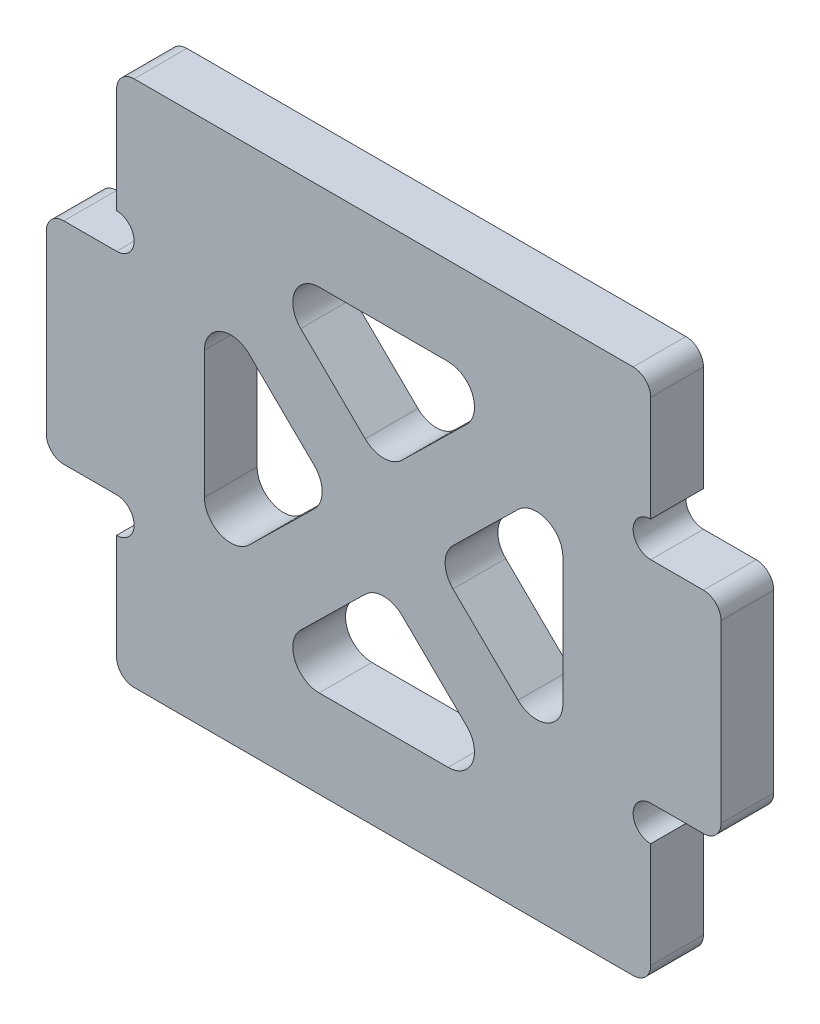
SolidWorks part; units mm, degrees
material "Thornel Mat VMA"
ref_plane "前视基准面" through (0, 0, 0) normal (0, 0, 1) x (1, 0, 0)
ref_plane "上视基准面" through (0, 0, 0) normal (0, 1, 0) x (1, 0, 0)
ref_plane "右视基准面" through (0, 0, 0) normal (1, 0, 0) x (0, 0, -1)
sketch "草图1" plane through (0, 0, 0) normal (0, 0, 1) x (1, 0, 0)
  line L0 (0, 0) -> (0, 28.9722) construction
  line L1 (15.2, -15) -> (-15.2, -15)
  line L2 (15.2, -15) -> (15.2, -6)
  line L3 (15.2, 15) -> (-15.2, 15)
  line L4 (-15.2, -15) -> (-15.2, -6)
  line L5 (15.2, -15) -> (-15.2, 15) construction
  line L6 (15.2, 15) -> (-15.2, -15) construction
  line L7 (0, 0) -> (-22.5864, 0) construction
  line L8 (15.2, -6) -> (19.2, -6)
  line L9 (-15.2, 6) -> (-19.2, 6)
  line L11 (-15.2, -6) -> (-19.2, -6)
  line L12 (-19.2, 6) -> (-19.2, -6)
  line L13 (19.2, 6) -> (19.2, -6)
  line L14 (15.2, 6) -> (19.2, 6)
  line L16 (-15.2, 6) -> (-15.2, 15)
  line L17 (15.2, 6) -> (15.2, 15)
  point P0 (0, 0)
  dimension "D1" = 30.4
  dimension "D2" = 30
  dimension "D3" = 4
  dimension "D4" = 12
extrude "凸台-拉伸1" add sketch "草图1" along normal blind 3 contours L12 L11 L4 L1 L2 L8 L13 L14 L17 L3 L16 L9
sketch "草图2" plane through (0, 0, 3) normal (0, 0, 1) x (1, 0, 0)
  line L0 (-15.2, 15) -> (-15.2, 6) construction
  line L1 (-15.2, -6) -> (-15.2, -15) construction
  line L2 (15.2, -15) -> (15.2, -6) construction
  line L3 (15.2, 6) -> (15.2, 15) construction
  circle A0 centre (-15.2, 7) radius 1
  circle A1 centre (-15.2, -7) radius 1
  circle A2 centre (15.2, -7) radius 1
  circle A3 centre (15.2, 7) radius 1
  dimension "D1" = 2
extrude "切除-拉伸1" cut sketch "草图2" against normal through all
sketch "草图3" plane through (0, 0, 3) normal (0, 0, 1) x (1, 0, 0)
  line L0 (15.2, 15) -> (-15.2, 15) construction
  line L1 (-10.2, 10) -> (10.2, 10)
  line L2 (-10.2, 10) -> (-10.2, -10)
  line L3 (-10.2, -10) -> (10.2, -10)
  line L4 (10.2, 10) -> (10.2, -10)
  line L5 (-15.2, 15) -> (-15.2, 8) construction
  line L6 (-15.2, -15) -> (15.2, -15) construction
  line L7 (15.2, 8) -> (15.2, 15) construction
  dimension "D1" = 5
  dimension "D2" = 5
  dimension "D3" = 5
  dimension "D4" = 5
extrude "切除-拉伸2" cut sketch "草图3" against normal through all
sketch "草图4" plane through (0, 0, 3) normal (0, 0, 1) x (1, 0, 0)
  line L0 (-10.2, 10) -> (10.2, -10)
  line L1 (-10.2, -10) -> (10.2, 10)
extrude "拉伸-薄壁1" add sketch "草图4" against normal up to surface (3 mm away) thin up to face at (0, 0, 0) thin type mid plane wall 4
fillet "圆角1" radius 1 8 edges at (19.2, -6, 1.5) (19.2, 6, 1.5) (15.2, 15, 1.5) (15.2, -15, 1.5) (-15.2, -15, 1.5) (-19.2, -6, 1.5) (-19.2, 6, 1.5) (-15.2, 15, 1.5)
fillet "圆角2" radius 1.5 12 edges at (0, -2.8008, 1.5) (7.3431, -10, 1.5) (-7.3431, -10, 1.5) (2.8569, 0, 1.5) (10.2, 7.1992, 1.5) (10.2, -7.1992, 1.5) (-2.8569, 0, 1.5) (-10.2, -7.1992, 1.5) (7.3431, 10, 1.5) (0, 2.8008, 1.5) (-7.3431, 10, 1.5) (-10.2, 7.1992, 1.5)
equation "\"1.51.00mm\"=1"
